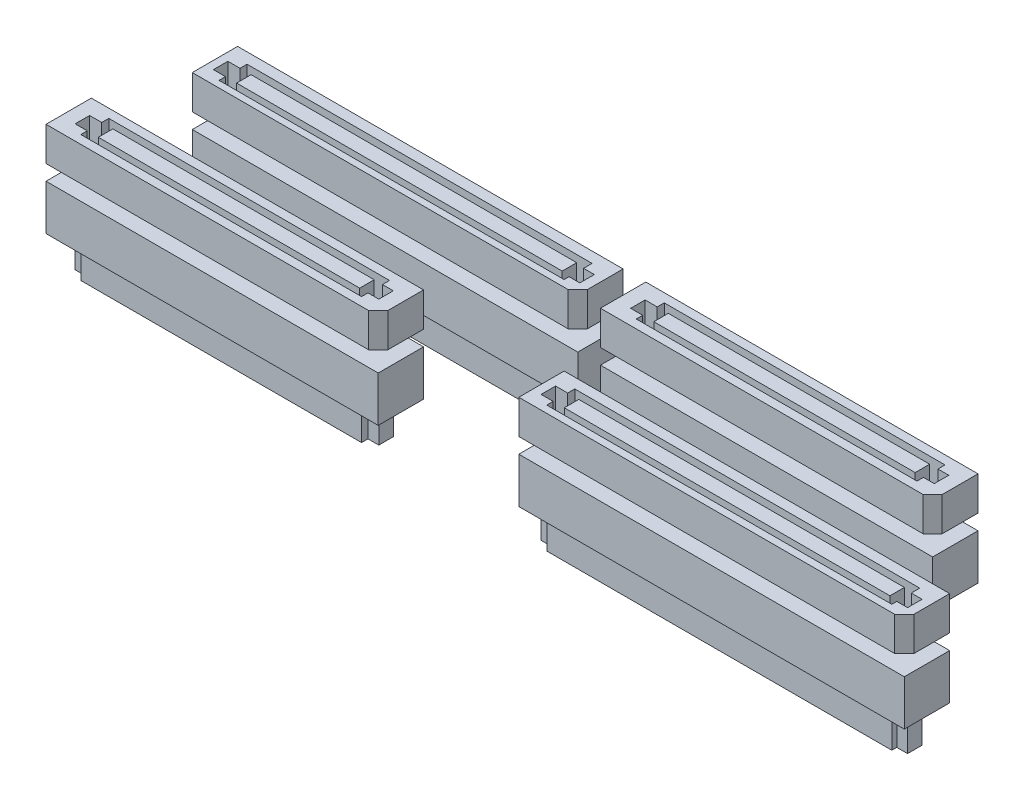
SolidWorks part; units mm, degrees
ref_plane "Front Plane" through (0, 0, 0) normal (0, 0, 1) x (1, 0, 0)
ref_plane "Top Plane" through (0, 0, 0) normal (0, 1, 0) x (1, 0, 0)
ref_plane "Right Plane" through (0, 0, 0) normal (1, 0, 0) x (0, 0, -1)
ref_plane "Plane1" through (0, -1.6866, 0) normal (0, 1, 0) x (1, 0, 0)
ref_plane "center-of-slot" through (0, -0.8433, 0) normal (0, 1, 0) x (1, 0, 0)
sketch "Sketch1" plane through (0, 0, 0) normal (0, 1, 0) x (1, 0, 0)
  line L0 (55.811, 9.5) -> (97.25, 9.5)
  line L1 (3.686, 9.5) -> (39.25, 9.5)
  line L2 (2.625, 8.439) -> (2.625, 4.5)
  line L3 (2.625, 4.5) -> (39.25, 4.5) construction
  line L4 (39.25, 9.5) -> (39.25, 4.5) construction
  line L5 (0, 0) -> (100, 0) construction
  line L6 (0, 0) -> (0, 75) construction
  line L7 (0, 75) -> (100, 75) construction
  line L8 (100, 0) -> (100, 75) construction
  line L9 (54.75, 8.439) -> (54.75, 4.5)
  line L10 (54.75, 4.5) -> (97.25, 4.5) construction
  line L11 (97.25, 9.5) -> (97.25, 4.5) construction
  line L12 (51.811, 22.5) -> (87.375, 22.5)
  line L13 (6.811, 22.5) -> (48.25, 22.5)
  line L14 (5.75, 21.439) -> (5.75, 17.5)
  line L15 (5.75, 17.5) -> (48.25, 17.5) construction
  line L16 (48.25, 22.5) -> (48.25, 17.5) construction
  line L17 (50.75, 21.439) -> (50.75, 17.5)
  line L18 (50.75, 17.5) -> (87.375, 17.5) construction
  line L19 (87.375, 22.5) -> (87.375, 17.5) construction
  line L20 (5.75, 21.439) -> (6.811, 22.5) construction
  line L21 (50.75, 21.439) -> (51.811, 22.5) construction
  line L22 (54.75, 8.439) -> (55.811, 9.5) construction
  line L23 (2.625, 8.439) -> (3.686, 9.5) construction
  line L24 (2.625, 4.5) -> (38.195, 4.5)
  line L25 (38.195, 4.5) -> (39.25, 5.555)
  line L26 (39.25, 5.555) -> (39.25, 9.5)
  line L27 (50.75, 17.5) -> (86.32, 17.5)
  line L28 (86.32, 17.5) -> (87.375, 18.555)
  line L29 (87.375, 18.555) -> (87.375, 22.5)
  line L30 (54.75, 4.5) -> (96.19, 4.5)
  line L31 (96.19, 4.5) -> (97.25, 5.56)
  line L32 (97.25, 5.56) -> (97.25, 9.5)
  line L33 (5.75, 17.5) -> (47.19, 17.5)
  line L34 (47.19, 17.5) -> (48.25, 18.56)
  line L35 (48.25, 18.56) -> (48.25, 22.5)
  line L36 (5.75, 21.439) -> (5.75, 22.5)
  line L37 (5.75, 22.5) -> (6.811, 22.5)
  line L38 (2.625, 8.439) -> (2.625, 9.5)
  line L39 (2.625, 9.5) -> (3.686, 9.5)
  line L40 (54.75, 8.439) -> (54.75, 9.5)
  line L41 (54.75, 9.5) -> (55.811, 9.5)
  line L42 (50.75, 21.439) -> (50.75, 22.5)
  line L43 (50.75, 22.5) -> (51.811, 22.5)
  point P0 (2.625, 9.5)
  point P9 (54.75, 9.5)
  point P13 (5.75, 22.5)
  point P17 (50.75, 22.5)
extrude "SV" add sketch "Sketch1" along normal blind 3.75
sketch "Sketch3" plane through (0, 3.75, 0) normal (0, 1, 0) x (1, 0, 0)
  line L0 (4.1893, 7.7457) -> (5.5243, 7.7457)
  line L1 (4.1893, 8.5242) -> (37.667, 8.5242) construction
  line L2 (4.1893, 8.5242) -> (4.1893, 5.4386) construction
  line L3 (4.1893, 5.4386) -> (37.667, 5.4386) construction
  line L4 (37.667, 8.5242) -> (37.667, 5.4386) construction
  line L5 (5.5243, 7.7457) -> (5.5243, 8.5242)
  line L6 (5.5243, 8.5242) -> (36.4757, 8.5242)
  line L7 (36.4757, 8.5242) -> (36.4757, 7.7457)
  line L8 (36.4757, 7.7457) -> (37.667, 7.7457)
  line L9 (37.667, 7.7457) -> (37.667, 6.1479)
  line L10 (37.667, 6.1479) -> (36.4757, 6.1479)
  line L11 (36.4757, 6.1479) -> (36.4757, 5.4386)
  line L12 (36.4757, 5.4386) -> (5.5243, 5.4386)
  line L13 (5.5243, 5.4386) -> (5.5243, 6.1479)
  line L14 (5.5243, 6.1479) -> (4.1893, 6.1479)
  line L15 (4.1893, 6.1479) -> (4.1893, 7.7457)
  line L16 (52.4211, 20.7536) -> (53.7561, 20.7536)
  line L17 (6.7471, 7.7457) -> (35.5588, 7.7457)
  line L18 (6.7471, 7.7457) -> (6.7471, 6.1479)
  line L19 (6.7471, 6.1479) -> (35.5588, 6.1479)
  line L20 (35.5588, 7.7457) -> (35.5588, 6.1479)
  line L21 (52.4211, 21.532) -> (85.8988, 21.532) construction
  line L22 (52.4211, 21.532) -> (52.4211, 18.4464) construction
  line L23 (52.4211, 18.4464) -> (85.8988, 18.4464) construction
  line L24 (85.8988, 21.532) -> (85.8988, 18.4464) construction
  line L25 (53.7561, 20.7536) -> (53.7561, 21.532)
  line L26 (53.7561, 21.532) -> (84.7075, 21.532)
  line L27 (84.7075, 21.532) -> (84.7075, 20.7536)
  line L28 (84.7075, 20.7536) -> (85.8988, 20.7536)
  line L29 (85.8988, 20.7536) -> (85.8988, 19.1558)
  line L30 (85.8988, 19.1558) -> (84.7075, 19.1558)
  line L31 (84.7075, 19.1558) -> (84.7075, 18.4464)
  line L32 (84.7075, 18.4464) -> (53.7561, 18.4464)
  line L33 (53.7561, 18.4464) -> (53.7561, 19.1558)
  line L34 (53.7561, 19.1558) -> (52.4211, 19.1558)
  line L35 (52.4211, 19.1558) -> (52.4211, 20.7536)
  line L36 (54.9789, 20.7536) -> (83.7906, 20.7536)
  line L37 (54.9789, 20.7536) -> (54.9789, 19.1558)
  line L38 (54.9789, 19.1558) -> (83.7906, 19.1558)
  line L39 (83.7906, 20.7536) -> (83.7906, 19.1558)
  line L40 (55.7059, 7.599) -> (57.0409, 7.599)
  line L41 (55.7059, 8.3775) -> (96.2696, 8.3775) construction
  line L42 (55.7059, 8.3775) -> (55.7059, 5.2919) construction
  line L43 (55.7059, 5.2919) -> (96.2696, 5.2919) construction
  line L44 (96.2696, 8.3775) -> (96.2696, 5.2919) construction
  line L45 (57.0409, 7.599) -> (57.0409, 8.3775)
  line L46 (57.0409, 8.3775) -> (95.0783, 8.3775)
  line L47 (95.0783, 8.3775) -> (95.0783, 7.4377)
  line L48 (95.0783, 7.4377) -> (96.2696, 7.4377)
  line L49 (96.2696, 7.4377) -> (96.2696, 5.8399)
  line L50 (96.2696, 5.8399) -> (95.0783, 5.8399)
  line L51 (95.0783, 5.8399) -> (95.0783, 5.2919)
  line L52 (95.0783, 5.2919) -> (57.0409, 5.2919)
  line L53 (57.0409, 5.2919) -> (57.0409, 6.0012)
  line L54 (57.0409, 6.0012) -> (55.7059, 6.0012)
  line L55 (55.7059, 6.0012) -> (55.7059, 7.599)
  line L56 (58.2637, 7.599) -> (94.1615, 7.599)
  line L57 (58.2637, 7.599) -> (58.2637, 6.0012)
  line L58 (58.2637, 6.0012) -> (94.1615, 6.0012)
  line L59 (94.1615, 7.599) -> (94.1615, 6.0012)
  line L60 (6.6366, 20.5397) -> (7.9716, 20.5397)
  line L61 (6.6366, 21.3182) -> (47.2003, 21.3182) construction
  line L62 (6.6366, 21.3182) -> (6.6366, 18.2325) construction
  line L63 (6.6366, 18.2325) -> (47.2003, 18.2325) construction
  line L64 (47.2003, 21.3182) -> (47.2003, 18.2325) construction
  line L65 (7.9716, 20.5397) -> (7.9716, 21.3182)
  line L66 (7.9716, 21.3182) -> (46.009, 21.3182)
  line L67 (46.009, 21.3182) -> (46.009, 20.3784)
  line L68 (46.009, 20.3784) -> (47.2003, 20.3784)
  line L69 (47.2003, 20.3784) -> (47.2003, 18.7806)
  line L70 (47.2003, 18.7806) -> (46.009, 18.7806)
  line L71 (46.009, 18.7806) -> (46.009, 18.2325)
  line L72 (46.009, 18.2325) -> (7.9716, 18.2325)
  line L73 (7.9716, 18.2325) -> (7.9716, 18.9419)
  line L74 (7.9716, 18.9419) -> (6.6366, 18.9419)
  line L75 (6.6366, 18.9419) -> (6.6366, 20.5397)
  line L76 (9.1944, 20.5397) -> (45.0922, 20.5397)
  line L77 (9.1944, 20.5397) -> (9.1944, 18.9419)
  line L78 (9.1944, 18.9419) -> (45.0922, 18.9419)
  line L79 (45.0922, 20.5397) -> (45.0922, 18.9419)
extrude "Cut-Extrude1" cut sketch "Sketch3" against normal blind 3.5
sketch "Sketch6" plane through (0, -1.6866, 0) normal (0, 1, 0) x (1, 0, 0)
  line L0 (2.625, 4.5) -> (2.625, 9.5) construction
  line L1 (5.75, 22.5) -> (48.25, 22.5) construction
  line L2 (5.75, 22.5) -> (5.75, 17.5) construction
  line L3 (5.75, 17.5) -> (48.25, 17.5) construction
  line L4 (48.25, 22.5) -> (48.25, 17.5) construction
  line L5 (50.75, 22.5) -> (87.375, 22.5) construction
  line L6 (50.75, 22.5) -> (50.75, 17.5) construction
  line L7 (50.75, 17.5) -> (87.375, 17.5) construction
  line L8 (87.375, 22.5) -> (87.375, 17.5) construction
  line L9 (97.25, 9.5) -> (54.75, 9.5) construction
  line L10 (97.25, 9.5) -> (97.25, 4.5) construction
  line L11 (97.25, 4.5) -> (54.75, 4.5) construction
  line L12 (54.75, 9.5) -> (54.75, 4.5) construction
  line L13 (39.25, 9.5) -> (2.625, 9.5) construction
  line L14 (39.25, 9.5) -> (39.25, 4.5) construction
  line L15 (39.25, 4.5) -> (2.625, 4.5) construction
  line L16 (2.625, 9.5) -> (2.625, 4.5) construction
  line L17 (2.625, 4.5) -> (38.195, 4.5)
  line L18 (2.625, 9.5) -> (39.25, 9.5) construction
  line L19 (48.25, 18.5619) -> (47.1881, 17.5) construction
  line L20 (39.25, 5.555) -> (39.25, 9.5)
  line L21 (48.25, 18.5619) -> (48.25, 22.5)
  line L22 (47.1881, 17.5) -> (5.75, 17.5)
  line L23 (39.25, 5.555) -> (38.195, 4.5) construction
  line L24 (54.75, 4.5) -> (96.19, 4.5)
  line L25 (96.19, 4.5) -> (97.25, 5.56) construction
  line L26 (97.25, 5.56) -> (97.25, 9.5)
  line L27 (50.75, 17.5) -> (86.32, 17.5)
  line L28 (86.32, 17.5) -> (87.375, 18.555) construction
  line L29 (87.375, 18.555) -> (87.375, 22.5)
  line L30 (2.625, 4.5) -> (2.625, 8.44)
  line L31 (2.625, 8.44) -> (3.685, 9.5)
  line L32 (3.685, 9.5) -> (39.25, 9.5)
  line L33 (5.75, 17.5) -> (5.75, 21.44)
  line L34 (5.75, 21.44) -> (6.81, 22.5)
  line L35 (6.81, 22.5) -> (48.25, 22.5)
  line L36 (54.75, 4.5) -> (54.75, 8.44)
  line L37 (54.75, 8.44) -> (55.81, 9.5)
  line L38 (55.81, 9.5) -> (97.25, 9.5)
  line L39 (87.375, 22.5) -> (51.805, 22.5)
  line L40 (51.805, 22.5) -> (50.75, 21.445)
  line L41 (50.75, 21.445) -> (50.75, 17.5)
  line L42 (47.1881, 17.5) -> (48.25, 17.5)
  line L43 (48.25, 17.5) -> (48.25, 18.5619)
  line L44 (38.195, 4.5) -> (39.25, 4.5)
  line L45 (39.25, 4.5) -> (39.25, 5.555)
  line L46 (96.19, 4.5) -> (97.25, 4.5)
  line L47 (97.25, 4.5) -> (97.25, 5.56)
  line L48 (86.32, 17.5) -> (87.375, 17.5)
  line L49 (87.375, 17.5) -> (87.375, 18.555)
  point P0 (5.75, 22.5)
  point P6 (50.75, 22.5)
  point P15 (54.75, 9.5)
extrude "SV4(a)" add sketch "Sketch6" against normal blind 5 separate body
sketch "Sketch7" plane through (0, -6.6866, 0) normal (0, -1, 0) x (1, 0, 0)
  line L0 (7.9716, -21.3182) -> (7.9716, -20.5397)
  line L1 (7.9716, -20.5397) -> (6.6366, -20.5397)
  line L2 (6.6366, -20.5397) -> (6.6366, -18.9419)
  line L3 (6.6366, -18.9419) -> (7.9716, -18.9419)
  line L4 (7.9716, -18.9419) -> (7.9716, -18.2325)
  line L6 (7.9716, -18.2325) -> (46.009, -18.2325)
  line L7 (46.009, -18.2325) -> (46.009, -18.7806)
  line L8 (46.009, -18.7806) -> (47.2003, -18.7806)
  line L9 (47.2003, -18.7806) -> (47.2003, -20.3784)
  line L10 (47.2003, -20.3784) -> (46.009, -20.3784)
  line L11 (46.009, -20.3784) -> (46.009, -21.3182)
  line L12 (46.009, -21.3182) -> (7.9716, -21.3182)
  line L13 (53.7561, -21.532) -> (84.7075, -21.532)
  line L14 (9.1944, -20.5397) -> (45.0922, -20.5397)
  line L15 (9.1944, -20.5397) -> (9.1944, -18.9419)
  line L16 (9.1944, -18.9419) -> (45.0922, -18.9419)
  line L17 (45.0922, -20.5397) -> (45.0922, -18.9419)
  line L18 (54.9789, -20.7536) -> (83.7906, -20.7536)
  line L19 (54.9789, -20.7536) -> (54.9789, -19.1558)
  line L20 (54.9789, -19.1558) -> (83.7906, -19.1558)
  line L21 (83.7906, -20.7536) -> (83.7906, -19.1558)
  line L22 (94.1615, -7.599) -> (58.2637, -7.599)
  line L23 (94.1615, -7.599) -> (94.1615, -6.0012)
  line L24 (94.1615, -6.0012) -> (58.2637, -6.0012)
  line L25 (58.2637, -7.599) -> (58.2637, -6.0012)
  line L26 (35.5588, -7.7457) -> (6.7471, -7.7457)
  line L27 (35.5588, -7.7457) -> (35.5588, -6.1479)
  line L28 (35.5588, -6.1479) -> (6.7471, -6.1479)
  line L29 (6.7471, -7.7457) -> (6.7471, -6.1479)
  line L30 (84.7075, -21.532) -> (84.7075, -20.7536)
  line L31 (84.7075, -20.7536) -> (85.8988, -20.7536)
  line L32 (85.8988, -20.7536) -> (85.8988, -19.1558)
  line L33 (85.8988, -19.1558) -> (84.7075, -19.1558)
  line L34 (84.7075, -19.1558) -> (84.7075, -18.4464)
  line L35 (84.7075, -18.4464) -> (53.7561, -18.4464)
  line L36 (53.7561, -18.4464) -> (53.7561, -19.1558)
  line L37 (53.7561, -19.1558) -> (52.4211, -19.1558)
  line L38 (52.4211, -19.1558) -> (52.4211, -20.7536)
  line L39 (52.4211, -20.7536) -> (53.7561, -20.7536)
  line L40 (53.7561, -20.7536) -> (53.7561, -21.532)
  line L41 (57.0409, -8.3775) -> (57.0409, -7.599)
  line L42 (57.0409, -7.599) -> (55.7059, -7.599)
  line L43 (55.7059, -7.599) -> (55.7059, -6.0012)
  line L44 (55.7059, -6.0012) -> (57.0409, -6.0012)
  line L45 (57.0409, -6.0012) -> (57.0409, -5.2919)
  line L46 (57.0409, -5.2919) -> (95.0783, -5.2919)
  line L47 (95.0783, -5.2919) -> (95.0783, -5.8399)
  line L48 (95.0783, -5.8399) -> (96.2696, -5.8399)
  line L49 (96.2696, -5.8399) -> (96.2696, -7.4377)
  line L50 (96.2696, -7.4377) -> (95.0783, -7.4377)
  line L51 (95.0783, -7.4377) -> (95.0783, -8.3775)
  line L52 (95.0783, -8.3775) -> (57.0409, -8.3775)
  line L53 (4.1893, -6.1479) -> (5.5243, -6.1479)
  line L54 (5.5243, -6.1479) -> (5.5243, -5.4386)
  line L55 (5.5243, -5.4386) -> (36.4757, -5.4386)
  line L56 (36.4757, -5.4386) -> (36.4757, -6.1479)
  line L57 (36.4757, -6.1479) -> (37.667, -6.1479)
  line L58 (37.667, -6.1479) -> (37.667, -7.7457)
  line L59 (37.667, -7.7457) -> (36.4757, -7.7457)
  line L60 (36.4757, -7.7457) -> (36.4757, -8.5242)
  line L61 (36.4757, -8.5242) -> (5.5243, -8.5242)
  line L62 (5.5243, -8.5242) -> (5.5243, -7.7457)
  line L63 (5.5243, -7.7457) -> (4.1893, -7.7457)
  line L64 (4.1893, -7.7457) -> (4.1893, -6.1479)
extrude "SV4(b)" add sketch "Sketch7" along normal blind 3.5
